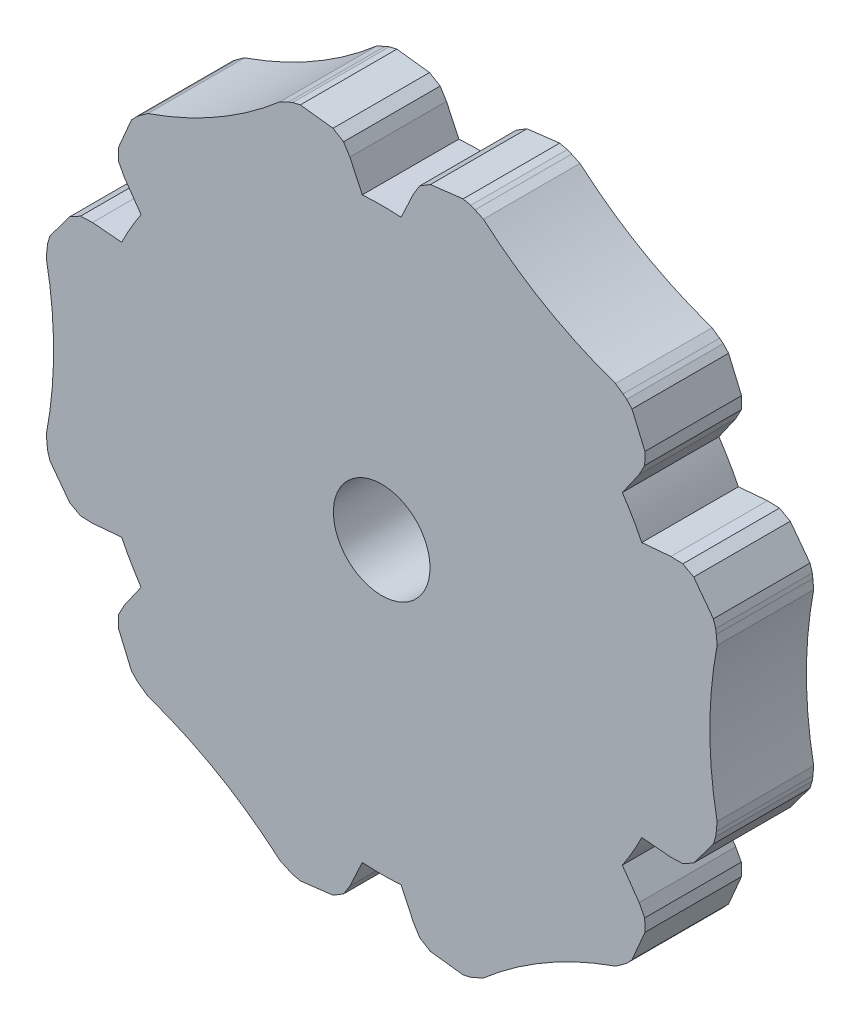
SolidWorks part; units mm, degrees
ref_plane "Front Plane" through (0, 0, 0) normal (0, 0, 1) x (1, 0, 0)
ref_plane "Top Plane" through (0, 0, 0) normal (0, 1, 0) x (1, 0, 0)
ref_plane "Right Plane" through (0, 0, 0) normal (1, 0, 0) x (0, 0, -1)
sketch "Sketch1" plane through (0, 0, 0) normal (0, 0, 1) x (1, 0, 0)
  line L0 (-131.9451, 33.8874) -> (-131.9451, -10.1126) construction
  line L1 (-152.3293, 11.8874) -> (-111.561, 11.8874) construction
  line L2 (-129.4832, -12.7318) -> (-129.756, -10.0034)
  line L3 (-134.407, -12.7318) -> (-134.1342, -10.0034)
  line L4 (-152.035, -2.5543) -> (-149.8086, -0.9538)
  line L5 (-154.4969, 1.7099) -> (-151.9977, 2.8378)
  line L6 (-154.4969, 22.0649) -> (-151.9977, 20.937)
  line L7 (-152.035, 26.3291) -> (-149.8086, 24.7286)
  line L8 (-134.407, 36.5066) -> (-134.1342, 33.7782)
  line L9 (-129.4832, 36.5066) -> (-129.756, 33.7782)
  line L10 (-111.8552, 26.3291) -> (-114.0817, 24.7286)
  line L11 (-109.3933, 22.0649) -> (-111.8926, 20.937)
  line L12 (-109.3933, 1.7099) -> (-111.8926, 2.8378)
  line L13 (-111.8552, -2.5543) -> (-114.0817, -0.9538)
  arc A1 (-151.9977, 2.8378) -> (-149.8086, -0.9538) centre (-131.9451, 11.8874) ccw
  arc A7 (-149.8086, 24.7286) -> (-151.9977, 20.937) centre (-131.9451, 11.8874) ccw
  arc A8 (-129.756, 33.7782) -> (-134.1342, 33.7782) centre (-131.9451, 11.8874) ccw
  arc A9 (-111.8926, 20.937) -> (-114.0817, 24.7286) centre (-131.9451, 11.8874) ccw
  arc A10 (-114.0817, -0.9538) -> (-111.8926, 2.8378) centre (-131.9451, 11.8874) ccw
  arc A11 (-134.1342, -10.0034) -> (-129.756, -10.0034) centre (-131.9451, 11.8874) ccw
  arc A13 (-109.3933, 22.0649) -> (-109.3933, 1.7099) centre (-86.585, 11.8874) ccw
  arc A14 (-111.8552, -2.5543) -> (-129.4832, -12.7318) centre (-109.2651, -27.3956) ccw
  arc A15 (-134.407, -12.7318) -> (-152.035, -2.5543) centre (-154.6252, -27.3956) ccw
  arc A16 (-154.4969, 1.7099) -> (-154.4969, 22.0649) centre (-177.3053, 11.8874) ccw
  arc A17 (-152.035, 26.3291) -> (-134.407, 36.5066) centre (-154.6252, 51.1705) ccw
  arc A18 (-129.4832, 36.5066) -> (-111.8552, 26.3291) centre (-109.2651, 51.1705) ccw
  circle A19 centre (-131.9451, 11.8874) radius 3
  point P6 (-109.1581, 1.6038)
  point P8 (-131.9451, 11.8874)
  point P11 (-109.1581, 22.1711)
  point P12 (-109.1581, 22.1711)
  point P13 (-131.9451, 11.8874)
  point P16 (-131.9451, 11.8874)
  point P19 (-131.9451, 11.8874)
  point P22 (-131.9451, 11.8874)
  point P25 (-131.9451, 11.8874)
  point P26 (-131.9451, 11.8874)
  point P53 (-131.9451, 11.8874)
  dimension "D1" = 6
  dimension "D2" = 6
extrude "Boss-Extrude2" add sketch "Sketch1" along normal blind 6
sketch "Sketch2" plane through (0, 0, 0) normal (0, 0, -1) x (-1, 0, 0)
  line L0 (131.9451, 33.8874) -> (131.9451, -10.1126) construction
  line L1 (133.1519, 29.847) -> (134.3655, 32.4475)
  line L2 (134.3655, 32.4475) -> (137.6585, 32.842)
  line L3 (130.7383, 29.847) -> (129.5247, 32.4475)
  line L4 (129.5247, 32.4475) -> (126.2318, 32.842)
  line L5 (150.9608, 20.0713) -> (152.949, 17.4168)
  line L6 (148.1019, 19.8221) -> (150.9608, 20.0713)
  line L7 (146.8951, 21.9123) -> (148.5405, 24.2636)
  line L8 (148.5405, 24.2636) -> (147.2357, 27.3126)
  line L9 (148.5405, -0.4887) -> (147.2357, -3.5378)
  line L10 (146.8951, 1.8625) -> (148.5405, -0.4887)
  line L11 (148.1019, 3.9528) -> (150.9608, 3.7035)
  line L12 (150.9608, 3.7035) -> (152.949, 6.358)
  line L13 (129.5247, -8.6726) -> (126.2318, -9.0672)
  line L14 (130.7383, -6.0721) -> (129.5247, -8.6726)
  line L15 (133.1519, -6.0721) -> (134.3655, -8.6726)
  line L16 (134.3655, -8.6726) -> (137.6585, -9.0672)
  line L17 (112.9294, 3.7035) -> (110.9412, 6.358)
  line L18 (115.7883, 3.9528) -> (112.9294, 3.7035)
  line L19 (116.9951, 1.8625) -> (115.3498, -0.4887)
  line L20 (115.3498, -0.4887) -> (116.6546, -3.5378)
  line L21 (115.3498, 24.2636) -> (116.6546, 27.3126)
  line L22 (116.9951, 21.9123) -> (115.3498, 24.2636)
  line L23 (115.7883, 19.8221) -> (112.9294, 20.0713)
  line L24 (112.9294, 20.0713) -> (110.9412, 17.4168)
  arc A0 (134.1342, 33.7782) -> (129.756, 33.7782) centre (131.9451, 11.8874) ccw construction
  arc A1 (129.756, -10.0034) -> (134.1342, -10.0034) centre (131.9451, 11.8874) ccw construction
  circle A2 centre (131.9451, 11.8874) radius 18
  arc A3 (134.407, 36.5066) -> (152.035, 26.3291) centre (154.6252, 51.1705) ccw construction
  point P51 (131.9451, 11.8874)
  arc M1 (134.1342, 33.7782) -> (129.756, 33.7782) centre (131.9451, 11.8874) ccw
  line M2 (129.756, 33.7782) -> (129.4832, 36.5066)
  arc M3 (129.4832, 36.5066) -> (111.8552, 26.3291) centre (109.2651, 51.1705) cw
  line M4 (111.8552, 26.3291) -> (114.0817, 24.7286)
  arc M5 (114.0817, 24.7286) -> (111.8926, 20.937) centre (131.9451, 11.8874) ccw
  line M6 (111.8926, 20.937) -> (109.3933, 22.0649)
  arc M7 (109.3933, 22.0649) -> (109.3933, 1.7099) centre (86.585, 11.8874) cw
  line M8 (109.3933, 1.7099) -> (111.8926, 2.8378)
  arc M9 (111.8926, 2.8378) -> (114.0817, -0.9538) centre (131.9451, 11.8874) ccw
  line M10 (114.0817, -0.9538) -> (111.8552, -2.5543)
  arc M11 (111.8552, -2.5543) -> (129.4832, -12.7318) centre (109.2651, -27.3956) cw
  line M12 (129.4832, -12.7318) -> (129.756, -10.0034)
  arc M13 (129.756, -10.0034) -> (134.1342, -10.0034) centre (131.9451, 11.8874) ccw
  line M14 (134.1342, -10.0034) -> (134.407, -12.7318)
  arc M15 (134.407, -12.7318) -> (152.035, -2.5543) centre (154.6252, -27.3956) cw
  line M16 (152.035, -2.5543) -> (149.8086, -0.9538)
  arc M17 (149.8086, -0.9538) -> (151.9977, 2.8378) centre (131.9451, 11.8874) ccw
  line M18 (151.9977, 2.8378) -> (154.4969, 1.7099)
  arc M19 (154.4969, 1.7099) -> (154.4969, 22.0649) centre (177.3053, 11.8874) cw
  line M20 (154.4969, 22.0649) -> (151.9977, 20.937)
  arc M21 (151.9977, 20.937) -> (149.8086, 24.7286) centre (131.9451, 11.8874) ccw
  line M22 (149.8086, 24.7286) -> (152.035, 26.3291)
  arc M23 (152.035, 26.3291) -> (134.407, 36.5066) centre (154.6252, 51.1705) cw
  line M24 (134.407, 36.5066) -> (134.1342, 33.7782)
  dimension "D1" = 6
extrude "Cut-Extrude1" cut sketch "Sketch2" against normal through all contours L0 A2 L1 L2 M1 M23 M24 | L0 L4 L3 A2 M1 M2 M3 | A2 L22 L21 L24 L23 M3 M4 M5 M6 M7 | A2 L18 L17 L20 L19 M7 M8 M9 M10 M11 | L0 A2 L14 L13 M11 M12 M13 | A2 L0 L16 L15 M13 M14 M15 | A2 L10 L9 L12 L11 M15 M16 M17 M18 M19 | A2 L6 L5 L8 L7 M19 M20 M21 M22 M23
sketch "Sketch5" plane through (0, 0, 0) normal (0, 0, -1) x (-1, 0, 0)
  line L0 (130.2055, 31.1195) -> (129.575, 32.1215)
  line L1 (129.575, 32.1215) -> (129.3109, 32.2817)
  line L2 (129.3109, 32.2817) -> (128.6973, 32.6541)
  line L3 (128.6973, 32.6541) -> (127.3663, 32.8739)
  line L4 (127.3663, 32.8739) -> (126.4162, 32.6541)
  line L5 (126.4162, 32.6541) -> (126.1474, 32.5426)
  line L6 (126.1474, 32.5426) -> (125.2188, 32.1113)
  line L7 (125.2188, 32.1113) -> (126.1474, 39.6128)
  line L8 (126.1474, 39.6128) -> (129.8902, 35.3413)
  line L9 (129.8902, 35.3413) -> (130.2055, 31.1195)
  line L10 (131.9451, 29.8875) -> (131.9451, -6.1126) construction
  line L11 (137.7428, 39.6128) -> (134, 35.3413)
  line L12 (138.6714, 32.1113) -> (137.7428, 39.6128)
  line L13 (137.7428, 32.5426) -> (138.6714, 32.1113)
  line L14 (137.474, 32.6541) -> (137.7428, 32.5426)
  line L15 (136.524, 32.8739) -> (137.474, 32.6541)
  line L16 (135.193, 32.6541) -> (136.524, 32.8739)
  line L17 (134.5793, 32.2817) -> (135.193, 32.6541)
  line L18 (134.3153, 32.1215) -> (134.5793, 32.2817)
  line L19 (133.6847, 31.1195) -> (134.3153, 32.1215)
  line L20 (134, 35.3413) -> (133.6847, 31.1195)
  line L21 (151.5535, 19.4581) -> (152.4094, 18.4152)
  line L22 (152.4094, 18.4152) -> (152.6941, 17.4826)
  line L23 (152.6941, 17.4826) -> (152.7319, 17.1941)
  line L24 (152.7319, 17.1941) -> (152.8227, 16.1742)
  line L25 (152.8227, 16.1742) -> (158.8549, 20.7292)
  line L26 (158.8549, 20.7292) -> (153.2842, 21.8348)
  line L27 (153.2842, 21.8348) -> (149.4704, 19.9969)
  line L28 (149.4704, 19.9969) -> (150.6534, 19.9518)
  line L29 (150.6534, 19.9518) -> (150.9242, 19.8033)
  line L30 (150.9242, 19.8033) -> (151.5535, 19.4581)
  line L31 (148.29, 24.3659) -> (148.3057, 25.0835)
  line L32 (148.2833, 24.0571) -> (148.29, 24.3659)
  line L33 (147.7308, 23.01) -> (148.2833, 24.0571)
  line L34 (151.2293, 25.3939) -> (147.7308, 23.01)
  line L35 (153.0572, 30.7711) -> (151.2293, 25.3939)
  line L36 (146.0964, 27.8245) -> (153.0572, 30.7711)
  line L37 (146.9342, 27.236) -> (146.0964, 27.8245)
  line L38 (147.1652, 27.059) -> (146.9342, 27.236)
  line L39 (147.8305, 26.3461) -> (147.1652, 27.059)
  line L40 (148.3057, 25.0835) -> (147.8305, 26.3461)
  line L41 (148.3057, -1.3087) -> (147.8305, -2.5712)
  line L42 (147.8305, -2.5712) -> (147.1652, -3.2841)
  line L43 (147.1652, -3.2841) -> (146.9342, -3.4611)
  line L44 (146.9342, -3.4611) -> (146.0964, -4.0497)
  line L45 (146.0964, -4.0497) -> (153.0572, -6.9962)
  line L46 (153.0572, -6.9962) -> (151.2293, -1.6191)
  line L47 (151.2293, -1.6191) -> (147.7308, 0.7649)
  line L48 (147.7308, 0.7649) -> (148.2833, -0.2823)
  line L49 (148.2833, -0.2823) -> (148.29, -0.591)
  line L50 (148.29, -0.591) -> (148.3057, -1.3087)
  line L51 (150.9242, 3.9715) -> (151.5535, 4.3168)
  line L52 (150.6534, 3.823) -> (150.9242, 3.9715)
  line L53 (149.4704, 3.7779) -> (150.6534, 3.823)
  line L54 (153.2842, 1.9401) -> (149.4704, 3.7779)
  line L55 (158.8549, 3.0456) -> (153.2842, 1.9401)
  line L56 (152.8227, 7.6006) -> (158.8549, 3.0456)
  line L57 (152.7319, 6.5808) -> (152.8227, 7.6006)
  line L58 (152.6941, 6.2922) -> (152.7319, 6.5808)
  line L59 (152.4094, 5.3596) -> (152.6941, 6.2922)
  line L60 (151.5535, 4.3168) -> (152.4094, 5.3596)
  line L61 (128.6973, -8.8793) -> (127.3663, -9.0991)
  line L62 (127.3663, -9.0991) -> (126.4162, -8.8793)
  line L63 (126.4162, -8.8793) -> (126.1474, -8.7678)
  line L64 (126.1474, -8.7678) -> (125.2188, -8.3365)
  line L65 (125.2188, -8.3365) -> (126.1474, -15.838)
  line L66 (126.1474, -15.838) -> (129.8902, -11.5664)
  line L67 (129.8902, -11.5664) -> (130.2055, -7.3446)
  line L68 (130.2055, -7.3446) -> (129.575, -8.3467)
  line L69 (129.575, -8.3467) -> (129.3109, -8.5069)
  line L70 (129.3109, -8.5069) -> (128.6973, -8.8793)
  line L71 (134.5793, -8.5069) -> (135.193, -8.8793)
  line L72 (134.3153, -8.3467) -> (134.5793, -8.5069)
  line L73 (133.6847, -7.3446) -> (134.3153, -8.3467)
  line L74 (134, -11.5664) -> (133.6847, -7.3446)
  line L75 (137.7428, -15.838) -> (134, -11.5664)
  line L76 (138.6714, -8.3365) -> (137.7428, -15.838)
  line L77 (137.7428, -8.7678) -> (138.6714, -8.3365)
  line L78 (137.474, -8.8793) -> (137.7428, -8.7678)
  line L79 (136.524, -9.0991) -> (137.474, -8.8793)
  line L80 (135.193, -8.8793) -> (136.524, -9.0991)
  line L81 (112.3367, 4.3168) -> (111.4809, 5.3596)
  line L82 (111.4809, 5.3596) -> (111.1962, 6.2922)
  line L83 (111.1962, 6.2922) -> (111.1584, 6.5808)
  line L84 (111.1584, 6.5808) -> (111.0676, 7.6006)
  line L85 (111.0676, 7.6006) -> (105.0354, 3.0456)
  line L86 (105.0354, 3.0456) -> (110.606, 1.9401)
  line L87 (110.606, 1.9401) -> (114.4199, 3.7779)
  line L88 (114.4199, 3.7779) -> (113.2368, 3.823)
  line L89 (113.2368, 3.823) -> (112.966, 3.9715)
  line L90 (112.966, 3.9715) -> (112.3367, 4.3168)
  line L91 (115.6002, -0.591) -> (115.5845, -1.3087)
  line L92 (115.607, -0.2823) -> (115.6002, -0.591)
  line L93 (116.1595, 0.7649) -> (115.607, -0.2823)
  line L94 (112.6609, -1.6191) -> (116.1595, 0.7649)
  line L95 (110.833, -6.9962) -> (112.6609, -1.6191)
  line L96 (117.7939, -4.0497) -> (110.833, -6.9962)
  line L97 (116.956, -3.4611) -> (117.7939, -4.0497)
  line L98 (116.7251, -3.2841) -> (116.956, -3.4611)
  line L99 (116.0597, -2.5712) -> (116.7251, -3.2841)
  line L100 (115.5845, -1.3087) -> (116.0597, -2.5712)
  line L101 (115.5845, 25.0835) -> (116.0597, 26.3461)
  line L102 (116.0597, 26.3461) -> (116.7251, 27.059)
  line L103 (116.7251, 27.059) -> (116.956, 27.236)
  line L104 (116.956, 27.236) -> (117.7939, 27.8245)
  line L105 (117.7939, 27.8245) -> (110.833, 30.7711)
  line L106 (110.833, 30.7711) -> (112.6609, 25.3939)
  line L107 (112.6609, 25.3939) -> (116.1595, 23.01)
  line L108 (116.1595, 23.01) -> (115.607, 24.0571)
  line L109 (115.607, 24.0571) -> (115.6002, 24.3659)
  line L110 (115.6002, 24.3659) -> (115.5845, 25.0835)
  line L111 (112.966, 19.8033) -> (112.3367, 19.4581)
  line L112 (113.2368, 19.9518) -> (112.966, 19.8033)
  line L113 (114.4199, 19.9969) -> (113.2368, 19.9518)
  line L114 (110.606, 21.8348) -> (114.4199, 19.9969)
  line L115 (105.0354, 20.7292) -> (110.606, 21.8348)
  line L116 (111.0676, 16.1742) -> (105.0354, 20.7292)
  line L117 (111.1584, 17.1941) -> (111.0676, 16.1742)
  line L118 (111.1962, 17.4826) -> (111.1584, 17.1941)
  line L119 (111.4809, 18.4152) -> (111.1962, 17.4826)
  line L120 (112.3367, 19.4581) -> (111.4809, 18.4152)
  arc A0 (133.1519, 29.847) -> (130.7383, 29.847) centre (131.9451, 11.8874) ccw construction
  arc A1 (130.7383, -6.0721) -> (133.1519, -6.0721) centre (131.9451, 11.8874) ccw construction
  point P28 (131.9451, 11.8874)
  point P132 (131.9451, 11.8874)
  dimension "D1" = 6
extrude "Cut-Extrude2" cut sketch "Sketch5" against normal through all
